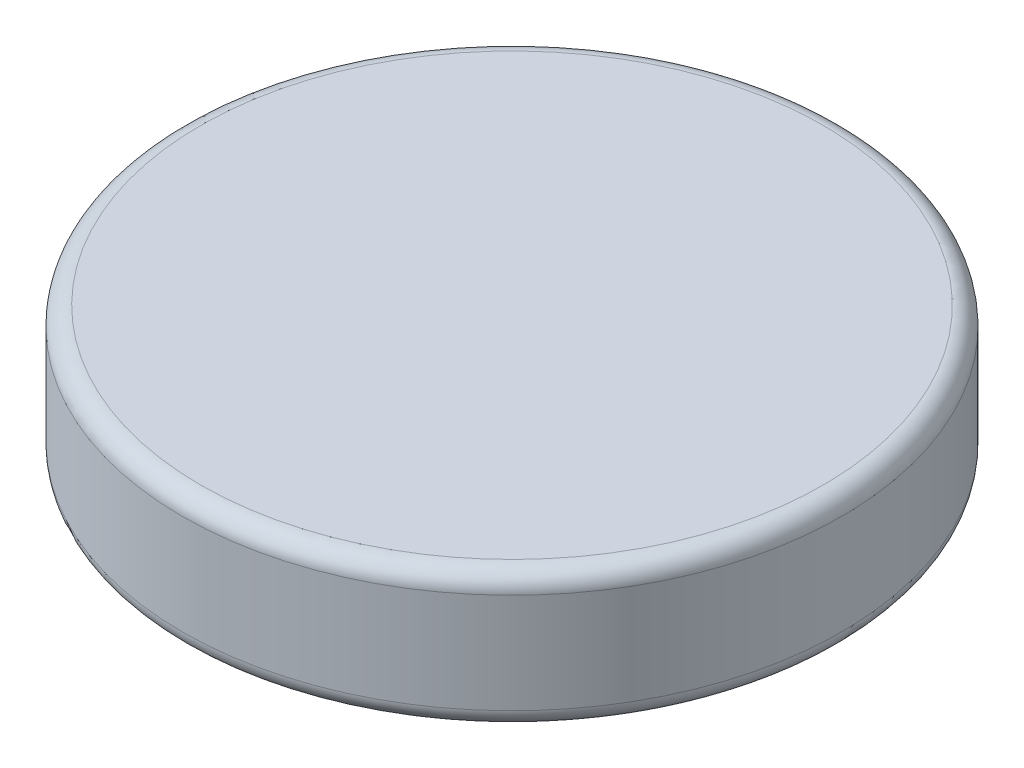
SolidWorks part; units mm, degrees
ref_plane "Front Plane" through (0, 0, 0) normal (0, 0, 1) x (1, 0, 0)
ref_plane "Top Plane" through (0, 0, 0) normal (0, 1, 0) x (1, 0, 0)
ref_plane "Right Plane" through (0, 0, 0) normal (1, 0, 0) x (0, 0, -1)
sketch "Sketch1" plane through (0, 0, 0) normal (0, 1, 0) x (1, 0, 0)
  circle A0 centre (0, 0) radius 184.15
  dimension "D1" = 368.3
extrude "Boss-Extrude1" add sketch "Sketch1" along normal blind 76.2
fillet "Fillet1" radius 10.16 2 edges at (0, 0, 184.15) (0, 76.2, 184.15)
